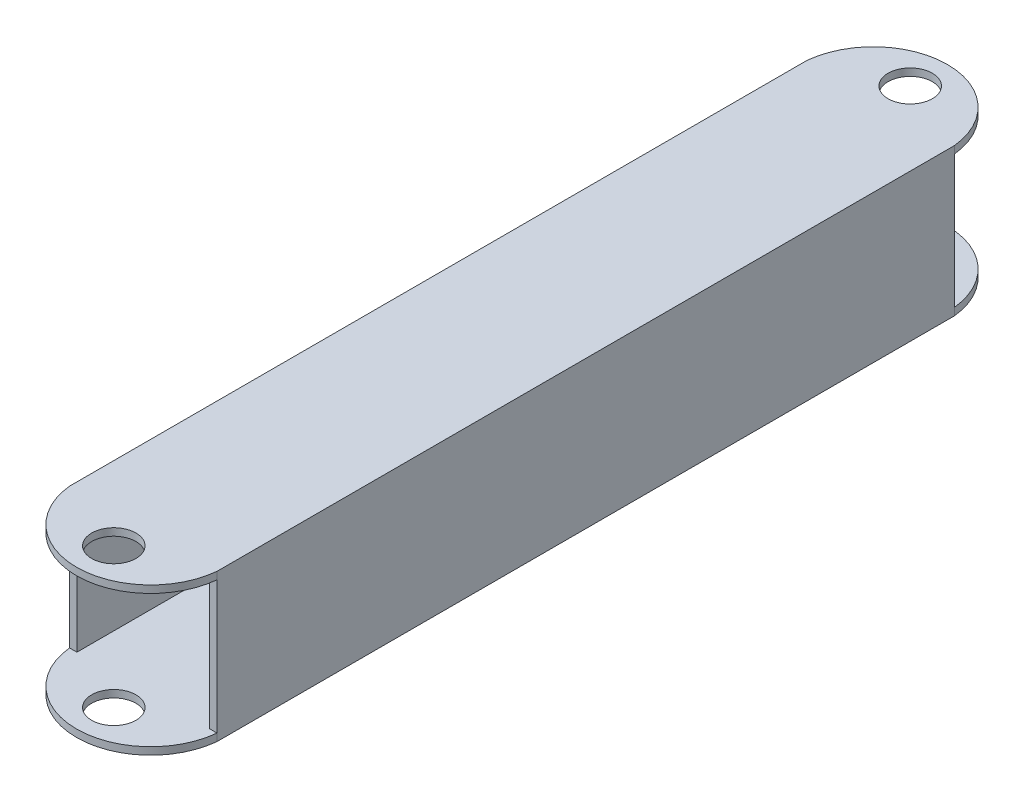
SolidWorks part; units mm, degrees
ref_plane "Front Plane" through (0, 0, 0) normal (0, 0, 1) x (1, 0, 0)
ref_plane "Top Plane" through (0, 0, 0) normal (0, 1, 0) x (1, 0, 0)
ref_plane "Right Plane" through (0, 0, 0) normal (1, 0, 0) x (0, 0, -1)
sketch "Sketch1" plane through (0, 0, 0) normal (0, 0, 1) x (1, 0, 0)
  line L0 (-9, 9) -> (9, 9)
  line L1 (-10, -10) -> (10, -10)
  line L2 (-10, -10) -> (-10, 10)
  line L3 (-10, 10) -> (10, 10)
  line L4 (10, -10) -> (10, 10)
  line L5 (-10, -10) -> (10, 10) construction
  line L6 (-10, 10) -> (10, -10) construction
  line L7 (9, -9) -> (9, 9)
  line L8 (-9, -9) -> (9, -9)
  line L9 (-9, -9) -> (-9, 9)
  point P0 (0, 0)
  dimension "D1" = 20
  dimension "D2" = 1
extrude "Boss-Extrude1" add sketch "Sketch1" along normal mid plane 100
sketch "Sketch2" plane through (0, -10, 0) normal (0, -1, 0) x (1, 0, 0)
  line L0 (-10, 50) -> (10, 50) construction
  line L1 (-10, 50) -> (10, 50)
  arc A0 (-10, 50) -> (10, 50) centre (0, 49) cw
  circle A1 centre (0, 54) radius 3
  point P9 (0, 44)
  dimension "D2" = 6
  dimension "D1" = 1
  dimension "D3" = 5
extrude "Boss-Extrude2" add sketch "Sketch2" against normal up to vertex
mirror "Mirror1" about plane through (0, 0, 0) normal (0, 0, 1) of "Boss-Extrude2"
mirror "Mirror2" about plane through (0, 0, 0) normal (0, 1, 0) of "Mirror1", "Boss-Extrude2"
